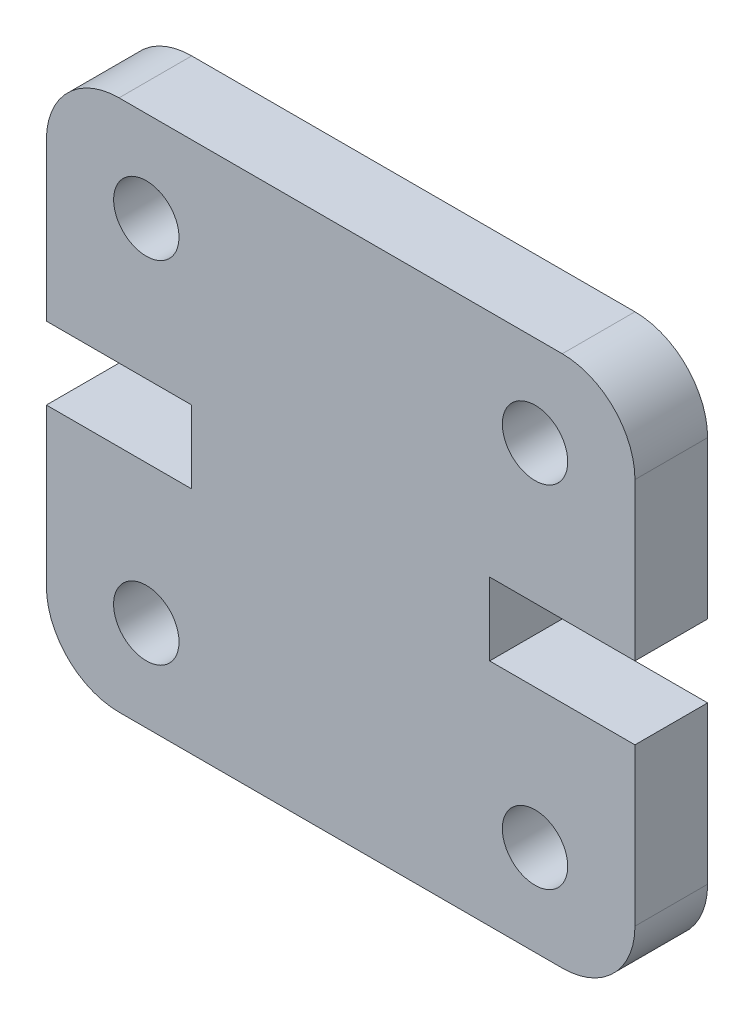
SolidWorks part; units mm, degrees
ref_plane "Front Plane" through (0, 0, 0) normal (0, 0, 1) x (1, 0, 0)
ref_plane "Top Plane" through (0, 0, 0) normal (0, 1, 0) x (1, 0, 0)
ref_plane "Right Plane" through (0, 0, 0) normal (1, 0, 0) x (0, 0, -1)
sketch "Sketch1" plane through (0, 0, 0) normal (0, 0, 1) x (1, 0, 0)
  line L0 (8.1, 14.645) -> (8.1, 0) construction
  line L1 (0, 7.3225) -> (16.2, 7.3225) construction
  line L2 (2, 14.645) -> (14.2, 14.645)
  line L3 (0, 8.3225) -> (4, 8.3225)
  line L4 (0, 8.3225) -> (0, 12.645)
  line L5 (12.2, 6.3225) -> (12.2, 8.3225)
  line L6 (16.2, 6.3225) -> (12.2, 6.3225)
  line L7 (16.2, 6.3225) -> (16.2, 2)
  line L8 (16.2, 8.3225) -> (16.2, 12.645)
  line L9 (16.2, 8.3225) -> (12.2, 8.3225)
  line L12 (0, 6.3225) -> (0, 2)
  line L17 (0, 6.3225) -> (4, 6.3225)
  line L18 (4, 6.3225) -> (4, 8.3225)
  line L19 (2, 0) -> (14.2, 0)
  circle A0 centre (2.75, 12.145) radius 0.9
  arc A1 (0, 12.645) -> (2, 14.645) centre (2, 12.645) cw
  circle A2 centre (13.45, 2.5) radius 0.9
  arc A3 (16.2, 2) -> (14.2, 0) centre (14.2, 2) cw
  arc A4 (16.2, 12.645) -> (14.2, 14.645) centre (14.2, 12.645) ccw
  circle A5 centre (13.45, 12.145) radius 0.9
  arc A11 (0, 2) -> (2, 0) centre (2, 2) ccw
  circle A13 centre (2.75, 2.5) radius 0.9
  point P9 (4, 7.3225)
  point P14 (8.1, 7.3225)
  point P27 (12.2, 7.3225)
  dimension "D1" = 1
  dimension "D2" = 2
  dimension "D8" = 1.8
  dimension "D3" = 2.75
  dimension "D4" = 8.1
  dimension "D5" = 2.5
  dimension "D6" = 6.3225
  dimension "D7" = 4
extrude "Boss-Extrude1" add sketch "Sketch1" along normal blind 4
sketch "Sketch2" plane through (0, 0, 0) normal (0, 0, -1) x (-1, 0, 0)
  line L0 (0, 0) -> (-16.2, 0)
  line L1 (-16.2, 0) -> (-16.2, 14.645)
  line L2 (-16.2, 14.645) -> (0, 14.645)
  line L3 (0, 14.645) -> (0, 0)
extrude "Cut-Extrude1" cut sketch "Sketch2" against normal blind 2
equation "\"D4@Sketch1\"= \"fingerWidth@parametersSketch@prostheticParameters.SLDPRT\" / 2'MIP width"
equation "\"D6@Sketch1\"=( \"HL@parametersSketch@prostheticParameters.SLDPRT\" * 0.117 - 4 - 3 - 2) / 2 'MIP length - Sil. Sht DIP - Sil. Sht MIP"
equation "\"D8@Sketch1\"= 1.5 + \"tol1@parametersSketch@prostheticParameters.SLDPRT\""
